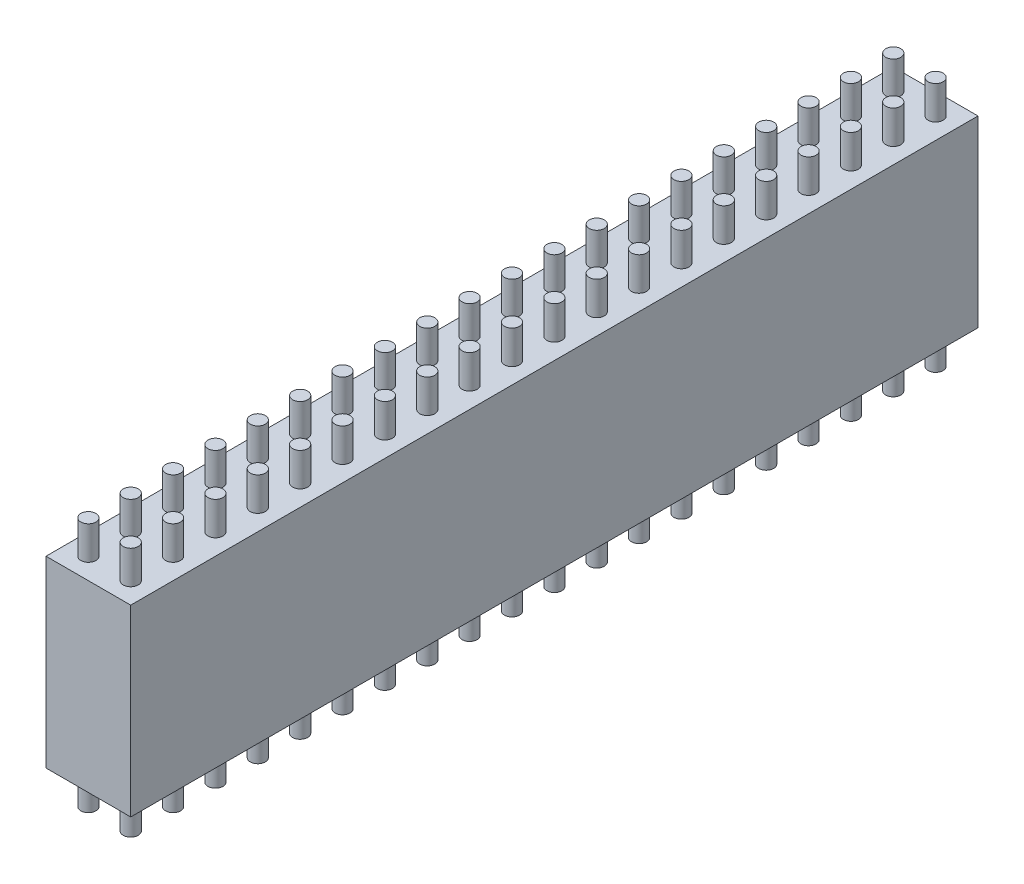
SolidWorks part; units mm, degrees
ref_plane "Ebene vorne" through (0, 0, 0) normal (0, 0, 1) x (1, 0, 0)
ref_plane "Ebene oben" through (0, 0, 0) normal (0, 1, 0) x (1, 0, 0)
ref_plane "Ebene rechts" through (0, 0, 0) normal (1, 0, 0) x (0, 0, -1)
sketch "Skizze1" plane through (0, 0, 0) normal (0, 1, 0) x (1, 0, 0)
  line L1 (0, 0) -> (5.08, 0)
  line L2 (0, 0) -> (0, 50.8)
  line L3 (0, 50.8) -> (5.08, 50.8)
  line L4 (5.08, 0) -> (5.08, 50.8)
  dimension "D1" = 50.8
  dimension "D2" = 5.08
extrude "Aufsatz-Linear austragen1" add sketch "Skizze1" along normal blind 11
sketch "Skizze2" plane through (0, 11, 0) normal (0, 1, 0) x (1, 0, 0)
  line L0 (0, 0) -> (5.08, 0) construction
  line L1 (0, 50.8) -> (0, 0) construction
  circle A0 centre (1.27, 1.27) radius 0.45
  circle A1 centre (3.81, 1.27) radius 0.45
  circle A2 centre (3.81, 3.81) radius 0.45
  circle A3 centre (3.81, 6.35) radius 0.45
  circle A4 centre (3.81, 8.89) radius 0.45
  circle A5 centre (3.81, 11.43) radius 0.45
  circle A6 centre (3.81, 13.97) radius 0.45
  circle A7 centre (3.81, 16.51) radius 0.45
  circle A8 centre (3.81, 19.05) radius 0.45
  circle A9 centre (3.81, 21.59) radius 0.45
  circle A10 centre (3.81, 24.13) radius 0.45
  circle A11 centre (1.27, 3.81) radius 0.45
  circle A12 centre (1.27, 6.35) radius 0.45
  circle A13 centre (1.27, 8.89) radius 0.45
  circle A14 centre (1.27, 11.43) radius 0.45
  circle A15 centre (1.27, 13.97) radius 0.45
  circle A16 centre (1.27, 16.51) radius 0.45
  circle A17 centre (1.27, 19.05) radius 0.45
  circle A18 centre (1.27, 21.59) radius 0.45
  circle A19 centre (1.27, 24.13) radius 0.45
  circle A20 centre (1.27, 26.67) radius 0.45
  circle A21 centre (3.81, 26.67) radius 0.45
  circle A22 centre (1.27, 29.21) radius 0.45
  circle A23 centre (3.81, 29.21) radius 0.45
  circle A24 centre (1.27, 31.75) radius 0.45
  circle A25 centre (3.81, 31.75) radius 0.45
  circle A26 centre (1.27, 34.29) radius 0.45
  circle A27 centre (3.81, 34.29) radius 0.45
  circle A28 centre (1.27, 36.83) radius 0.45
  circle A29 centre (3.81, 36.83) radius 0.45
  circle A30 centre (1.27, 39.37) radius 0.45
  circle A31 centre (3.81, 39.37) radius 0.45
  circle A32 centre (1.27, 41.91) radius 0.45
  circle A33 centre (3.81, 41.91) radius 0.45
  circle A34 centre (1.27, 44.45) radius 0.45
  circle A35 centre (3.81, 44.45) radius 0.45
  circle A36 centre (1.27, 46.99) radius 0.45
  circle A37 centre (3.81, 46.99) radius 0.45
  circle A38 centre (1.27, 49.53) radius 0.45
  circle A39 centre (3.81, 49.53) radius 0.45
  dimension "D3" = 0.9
  dimension "D1" = 1.27
  dimension "D2" = 1.27
  dimension "D6" = 2.54
  dimension "D7" = 2.54
  dimension "D4" = 2
  dimension "D5" = 20
extrude "Aufsatz-Linear austragen2" add sketch "Skizze2" along normal blind 2 and the other way blind 13
